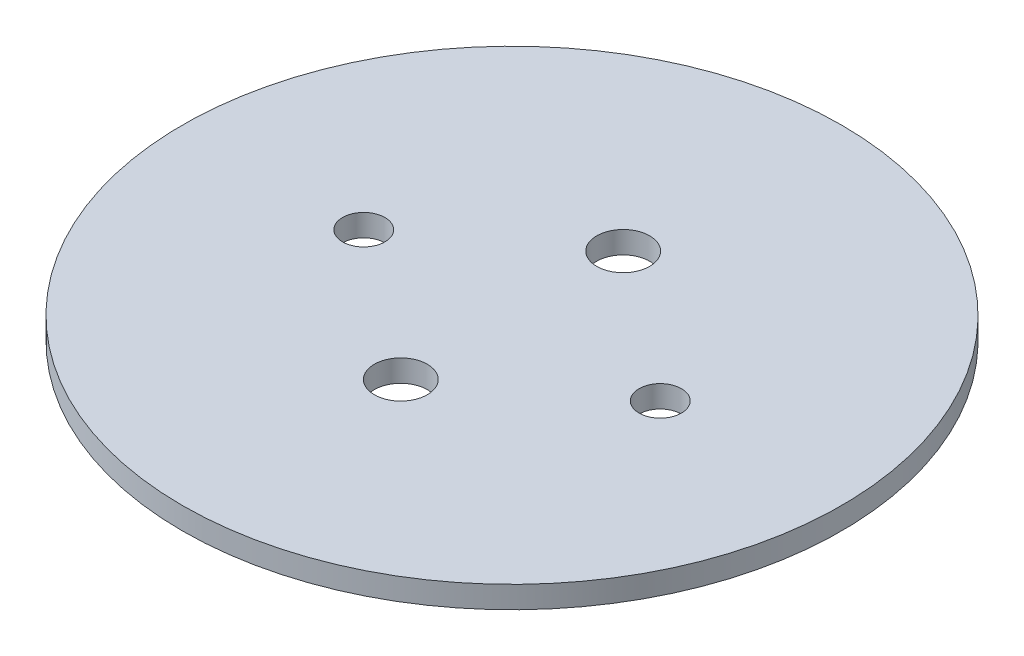
SolidWorks part; units mm, degrees
ref_plane "Front Plane" through (0, 0, 0) normal (0, 0, 1) x (1, 0, 0)
ref_plane "Top Plane" through (0, 0, 0) normal (0, 1, 0) x (1, 0, 0)
ref_plane "Right Plane" through (0, 0, 0) normal (1, 0, 0) x (0, 0, -1)
sketch "Sketch1" plane through (0, 0, 0) normal (0, 1, 0) x (1, 0, 0)
  line L0 (-22.225, 0) -> (22.225, 0) construction
  line L1 (0, 16.6687) -> (0, -16.6687) construction
  circle A0 centre (0, 0) radius 49.403
  circle A1 centre (22.225, 0) radius 3.175
  circle A2 centre (-22.225, 0) radius 3.175
  circle A3 centre (0, -16.6687) radius 3.9688
  circle A5 centre (0, 16.6687) radius 3.9688
  point P6 (0, 0)
  point P11 (0, 0)
  point P13 (0, 0)
  dimension "D1" = 6.35
  dimension "D2" = 98.806
  dimension "D5" = 7.9375
  dimension "D3" = 44.45
  dimension "D4" = 33.3375
extrude "Boss-Extrude1" add sketch "Sketch1" along normal blind 3.302
